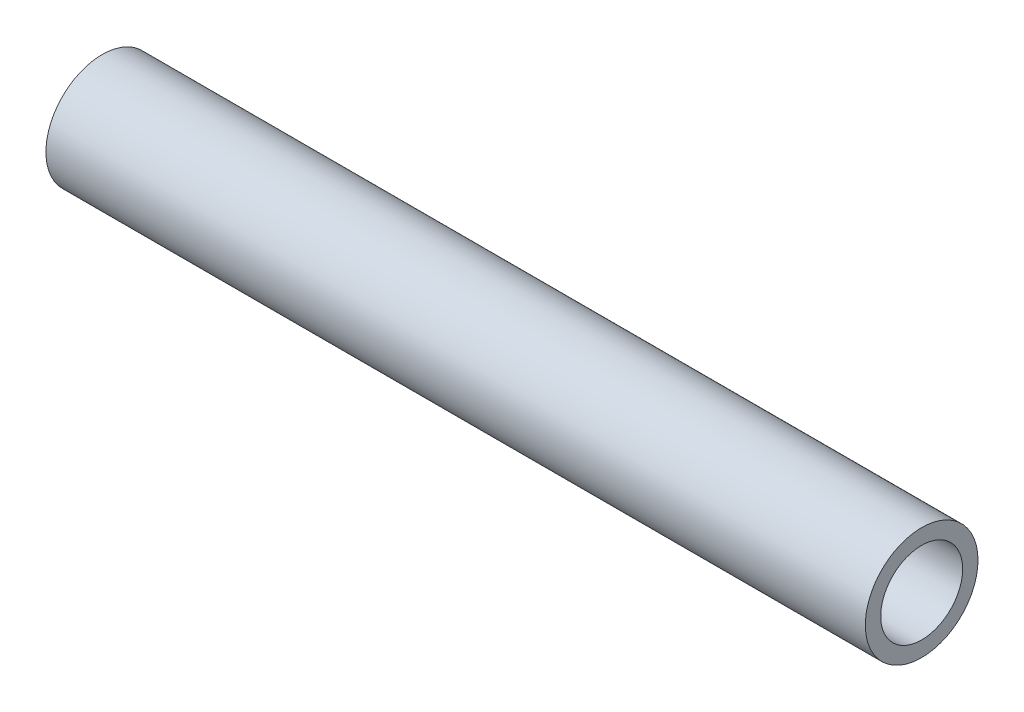
SolidWorks part; units mm, degrees
material "AISI 1045 Acier étiré à froid"
ref_plane "Plan de face" through (0, 0, 0) normal (0, 0, 1) x (1, 0, 0)
ref_plane "Plan de dessus" through (0, 0, 0) normal (0, 1, 0) x (1, 0, 0)
ref_plane "Plan de droite" through (0, 0, 0) normal (1, 0, 0) x (0, 0, -1)
sketch "Esquisse1" plane through (0, 0, 0) normal (1, 0, 0) x (0, 0, -1)
  circle A0 centre (0, 0) radius 8
  circle A1 centre (0, 0) radius 11
  dimension "D1" = 16
  dimension "D2" = 22
extrude "Boss.-Extru.1" add sketch "Esquisse1" along normal blind 160
